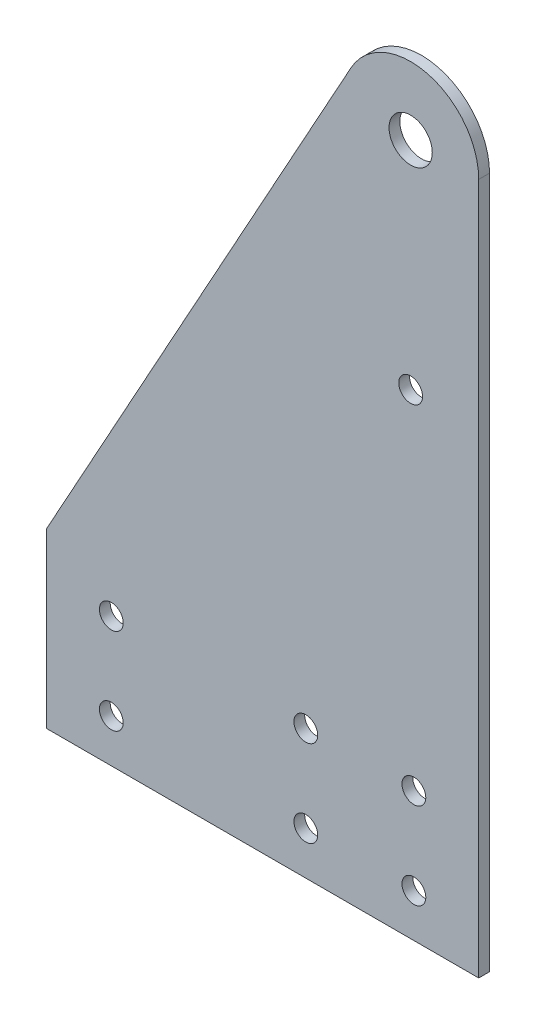
SolidWorks part; units mm, degrees
ref_plane "Front Plane" through (0, 0, 0) normal (0, 0, 1) x (1, 0, 0)
ref_plane "Top Plane" through (0, 0, 0) normal (0, 1, 0) x (1, 0, 0)
ref_plane "Right Plane" through (0, 0, 0) normal (1, 0, 0) x (0, 0, -1)
sketch "Sketch1" plane through (0, 0, 0) normal (0, 0, 1) x (1, 0, 0)
  line L0 (-63.5, -25.4) -> (63.5, -25.4)
  line L2 (63.5, -25.4) -> (63.5, 177.8)
  line L3 (25.9919, 187.4678) -> (-63.5, 25.4)
  line L5 (-63.5, 25.4) -> (-63.5, -25.4)
  line L6 (-63.5, 25.4) -> (63.5, -25.4) construction
  line L7 (44.45, 12.7) -> (12.7, 12.7) construction
  line L8 (-44.45, -12.7) -> (44.45, -12.7) construction
  line L9 (-44.45, -12.7) -> (-44.45, 12.7) construction
  line L10 (-44.45, 12.7) -> (44.45, 12.7) construction
  line L11 (44.45, -12.7) -> (44.45, 12.7) construction
  line L12 (-44.45, -12.7) -> (44.45, 12.7) construction
  line L13 (-44.45, 12.7) -> (44.45, -12.7) construction
  arc A0 (25.9919, 187.4678) -> (63.5, 177.8) centre (43.5, 177.8) cw
  circle A1 centre (43.5, 177.8) radius 6.35
  circle A2 centre (-44.45, 12.7) radius 3.5
  circle A3 centre (44.45, 12.7) radius 3.5
  circle A4 centre (44.45, -12.7) radius 3.5
  circle A5 centre (-44.45, -12.7) radius 3.5
  circle A6 centre (12.7, 12.7) radius 3.5
  circle A7 centre (12.7, -12.7) radius 3.5
  circle A8 centre (43.5, 114.3) radius 3.5
  point P7 (0, 0)
  point P8 (0, 0)
  dimension "D2" = 12.7
  dimension "D6" = 20
  dimension "D5" = 7
  dimension "D10" = 63.5
  dimension "D1" = 50.8
  dimension "D3" = 127
  dimension "D4" = 152.4
  dimension "D7" = 25.4
  dimension "D8" = 88.9
  dimension "D9" = 31.75
extrude "Boss-Extrude1" add sketch "Sketch1" along normal blind 3.175
